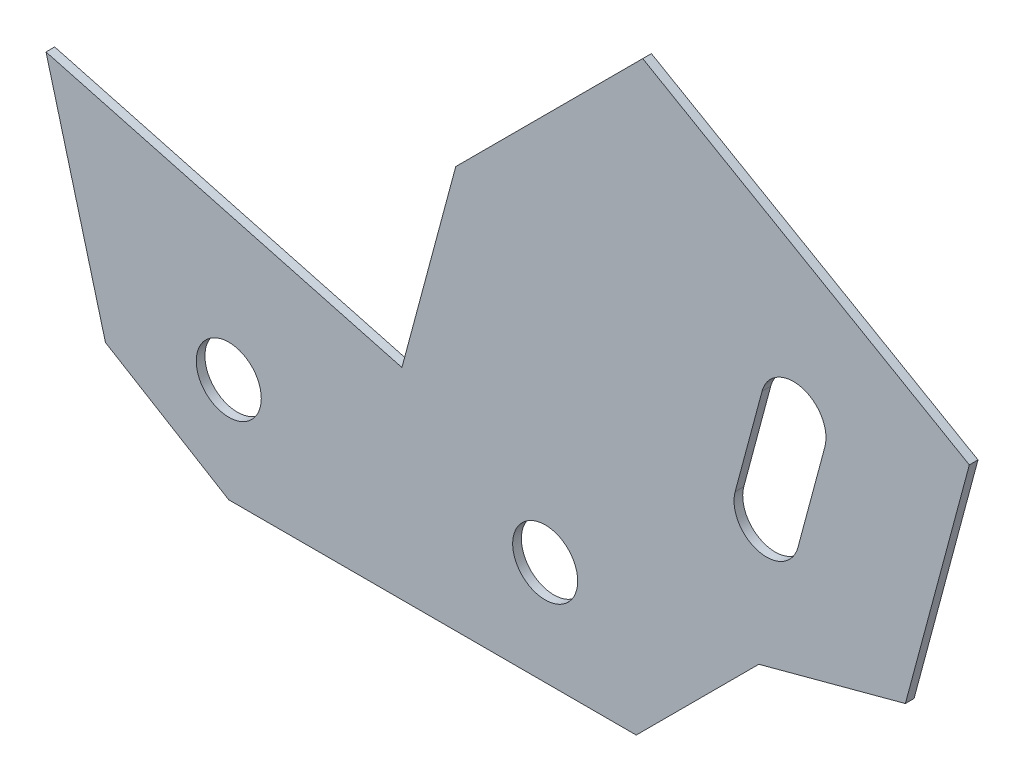
SolidWorks part; units mm, degrees
material "Alloy Steel"
ref_plane "Front Plane" through (0, 0, 0) normal (0, 0, 1) x (1, 0, 0)
ref_plane "Top Plane" through (0, 0, 0) normal (0, 1, 0) x (1, 0, 0)
ref_plane "Right Plane" through (0, 0, 0) normal (1, 0, 0) x (0, 0, -1)
sketch "Sketch1" plane through (0, 0, 0) normal (0, 0, 1) x (1, 0, 0)
  line L0 (-73, -24) -> (21, -24)
  line L1 (21, -24) -> (49.2843, 4.2843)
  line L2 (49.2843, 4.2843) -> (83.0917, 13.3429)
  line L3 (83.0917, 13.3429) -> (97.8444, 68.4007)
  line L4 (97.8444, 68.4007) -> (22.5002, 111.9007)
  line L5 (22.5002, 111.9007) -> (-20.6334, 68.7672)
  line L6 (-20.6334, 68.7672) -> (-33.0567, 22.4028)
  line L7 (-33.0567, 22.4028) -> (-115.1604, 44.4024)
  line L8 (-115.1604, 44.4024) -> (-101.443, -6.7917)
  line L9 (-101.443, -6.7917) -> (-73, -24)
  line L10 (57.2756, 57.2756) -> (51.064, 34.0934) construction
  line L11 (64.5201, 55.3345) -> (58.3084, 32.1523)
  line L12 (50.0312, 59.2168) -> (43.8195, 36.0346)
  line L13 (0, 0) -> (57.2756, 57.2756) construction
  line L14 (-73, 0) -> (0, 0) construction
  circle A0 centre (0, 0) radius 7.5
  circle A1 centre (-73, 0) radius 7.5
  arc A2 (64.5201, 55.3345) -> (50.0312, 59.2168) centre (57.2756, 57.2756) ccw
  arc A3 (43.8195, 36.0346) -> (58.3084, 32.1523) centre (51.064, 34.0934) ccw
  point P17 (54.1698, 45.6845)
  dimension "D1" = 15
  dimension "D2" = 73
  dimension "D3" = 24
  dimension "D4" = 94
  dimension "D5" = 135
  dimension "D6" = 40
  dimension "D7" = 35
  dimension "D8" = 150
  dimension "D9" = 57
  dimension "D10" = 120
  dimension "D11" = 87
  dimension "D12" = 105
  dimension "D13" = 61
  dimension "D14" = 105
  dimension "D15" = 48
  dimension "D16" = 150
  dimension "D17" = 90
  dimension "D18" = 85
  dimension "D19" = 53
  dimension "D20" = 60
  dimension "D21" = 24
  dimension "D22" = 15
  dimension "D23" = 81
  dimension "D24" = 30
  dimension "D25" = 135
extrude "Boss-Extrude1" add sketch "Sketch1" along normal blind 2
